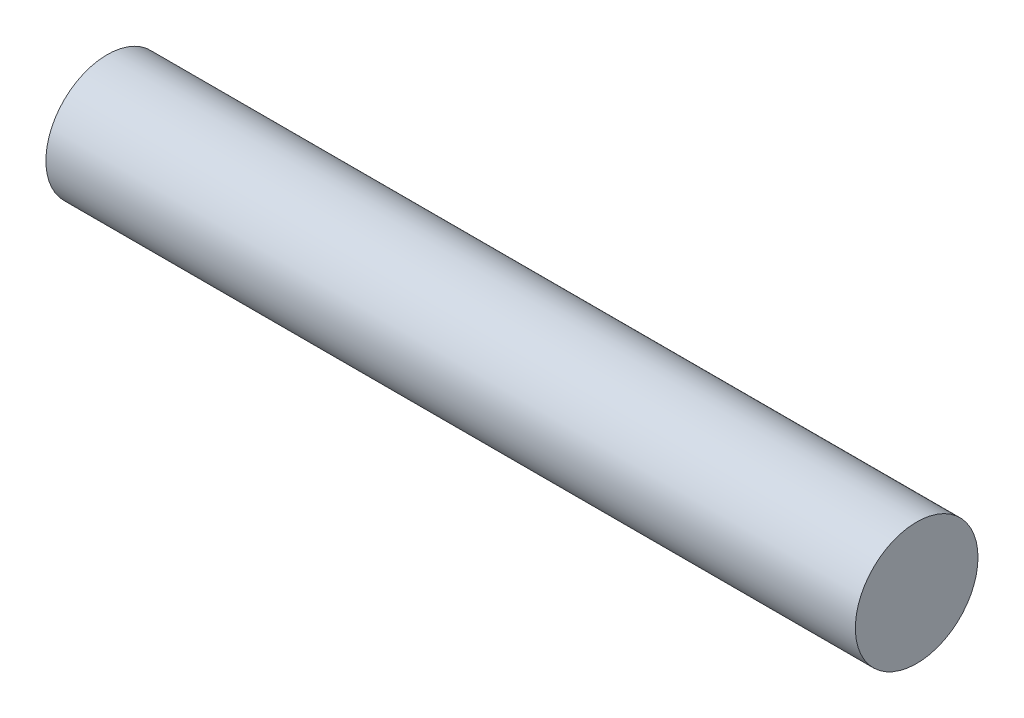
SolidWorks part; units mm, degrees
ref_plane "Front Plane" through (0, 0, 0) normal (0, 0, 1) x (1, 0, 0)
ref_plane "Top Plane" through (0, 0, 0) normal (0, 1, 0) x (1, 0, 0)
ref_plane "Right Plane" through (0, 0, 0) normal (1, 0, 0) x (0, 0, -1)
sketch "Sketch1" plane through (0, 0, 0) normal (1, 0, 0) x (0, 0, -1)
  circle A0 centre (0, 0) radius 3.175
  dimension "D1" = 6.35
extrude "Boss-Extrude1" add sketch "Sketch1" along normal blind 41.91
